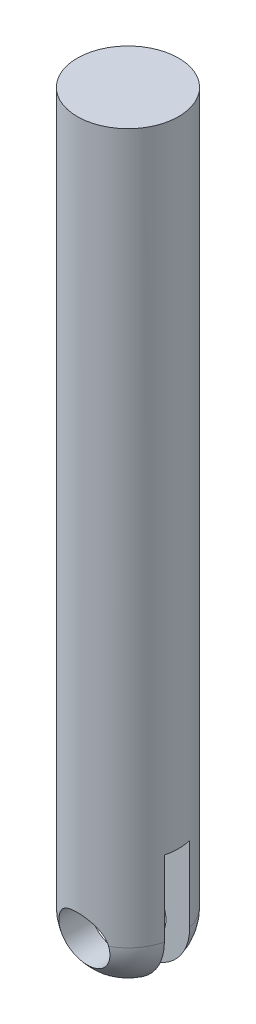
SolidWorks part; units mm, degrees
ref_plane "Front Plane" through (0, 0, 0) normal (0, 0, 1) x (1, 0, 0)
ref_plane "Top Plane" through (0, 0, 0) normal (0, 1, 0) x (1, 0, 0)
ref_plane "Right Plane" through (0, 0, 0) normal (1, 0, 0) x (0, 0, -1)
ref_plane "Plane1" through (0, 0, 2.5) normal (0, 0, -1) x (-1, 0, 0)
sketch "Sketch1" plane through (0, 0, 2.5) normal (0, 0, -1) x (-1, 0, 0)
  line L0 (0, 233.5) -> (0, 83.5)
  line L1 (0, 233.5) -> (10, 233.5)
  line L2 (10, 233.5) -> (10, 93.5)
  arc A0 (10, 93.5) -> (0, 83.5) centre (0, 93.5) cw
  circle A1 centre (0, 92.5) radius 5 construction
  dimension "D2" = 150
  dimension "D3" = 9
  dimension "D1" = 10
revolve "Revolve1" add sketch "Sketch1" angle 360 about L0
sketch "Sketch2" plane through (0, 0, 0) normal (1, 0, 0) x (0, 0, -1)
  line L0 (0, 41) -> (0, 80) construction
  line L1 (-5, 108.4006) -> (0, 108.4006)
  line L2 (-5, 108.4006) -> (-5, 75.018)
  line L3 (-5, 75.018) -> (0, 75.018)
  line L4 (0, 108.4006) -> (0, 75.018)
  line L5 (-5, 105) -> (-5, 80) construction
extrude "Cut-Extrude1" cut sketch "Sketch2" against normal through all and the other way through all
sketch "Sketch3" plane through (0, 0, 0) normal (0, 0, 1) x (1, 0, 0)
  circle A0 centre (0, 92.5) radius 5
  dimension "D1" = 10
extrude "Cut-Extrude2" cut sketch "Sketch3" against normal through all both and the other way through all
